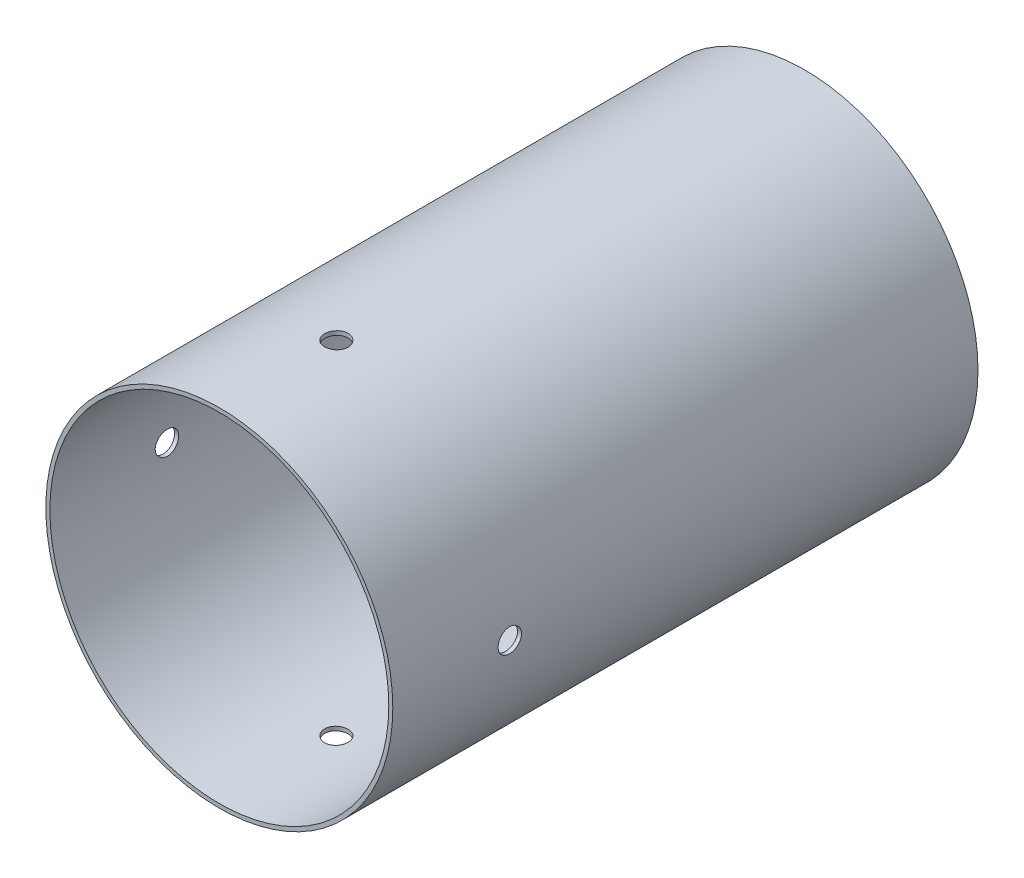
SolidWorks part; units mm, degrees
ref_plane "前基準面" through (0, 0, 0) normal (0, 0, 1) x (1, 0, 0)
ref_plane "上基準面" through (0, 0, 0) normal (0, 1, 0) x (1, 0, 0)
ref_plane "右基準面" through (0, 0, 0) normal (1, 0, 0) x (0, 0, -1)
sketch "草圖1" plane through (0, 0, 0) normal (0, 0, 1) x (1, 0, 0)
  circle A0 centre (0, 0) radius 148.209
  circle A1 centre (0, 0) radius 144.78
  dimension "D1" = 296.418
  dimension "D2" = 289.56
extrude "填料-伸長1" add sketch "草圖1" along normal blind 500
sketch "草圖2" plane through (0, 0, 0) normal (1, 0, 0) x (0, 0, -1)
  line L0 (-400, 177.6393) -> (-400, 120.6085) construction
  line L1 (0, 148.209) -> (-500, 148.209) construction
  line L2 (-410, 133.209) -> (-400, 133.209)
  line L3 (-410, 133.209) -> (-410, 163.209)
  line L4 (-410, 163.209) -> (-400, 163.209)
  line L5 (-400, 133.209) -> (-400, 163.209)
  line L6 (-410, 133.209) -> (-400, 163.209) construction
  line L7 (-410, 163.209) -> (-400, 133.209) construction
  line L8 (0, 163.0299) -> (0, -163.0299) construction
  point P2 (-405, 148.209)
  dimension "D1" = 20
  dimension "D2" = 400
  dimension "D3" = 30
revolve "除料-旋轉1" cut sketch "草圖2" angle 360 about L5
pattern_circular "環狀複製排列1" count 4 over 360 about axis through (0, 0, 500) along (0, 0, -1) of "除料-旋轉1"
